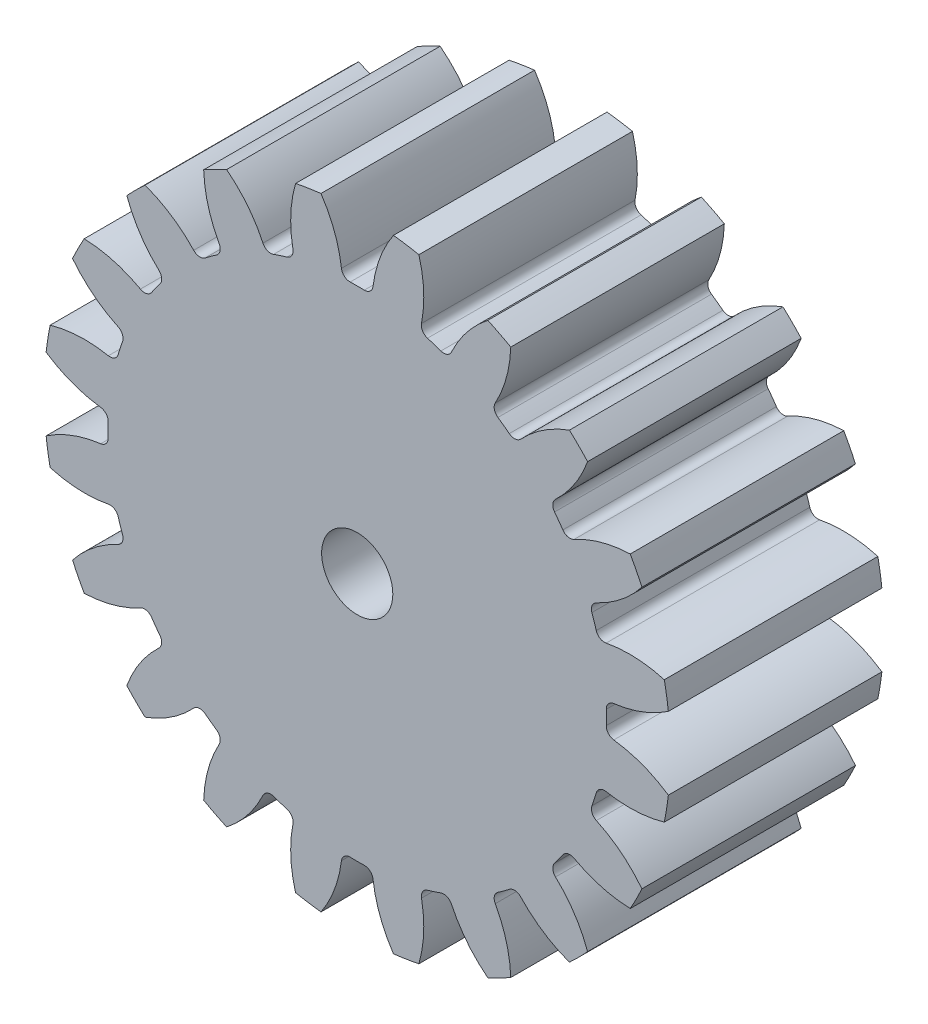
SolidWorks part; units mm, degrees
material "1023 Carbon Steel Sheet (SS)"
ref_plane "Front Plane" through (0, 0, 0) normal (0, 0, 1) x (1, 0, 0)
ref_plane "Top Plane" through (0, 0, 0) normal (0, 1, 0) x (1, 0, 0)
ref_plane "Right Plane" through (0, 0, 0) normal (1, 0, 0) x (0, 0, -1)
sketch "skBase" plane through (0, 0, 0) normal (0, 0, 1) x (1, 0, 0)
  circle A0 centre (0, 0) radius 20
  circle A1 centre (0, 0) radius 22
  circle A2 centre (0, 0) radius 17.5
  dimension "D1" = 40
  dimension "D3" = 4.5
extrude "Base" add sketch "skBase" along normal mid plane 15 contours A1
sketch "skToothProfile" plane through (0, 0, 0) normal (0, 0, 1) x (1, 0, 0)
  line L0 (0, 0) -> (0, 22) construction
  line L1 (-1.5692, 19.9383) -> (1.5692, 19.9383) construction
  line L2 (-1.0563, 17.4681) -> (0, 0) construction
  line L3 (0, 15.6271) -> (-2.6287, 22.8493) construction
  line L4 (0, 0) -> (3.4416, 21.7291) construction
  line L5 (1.5692, 19.9383) -> (4.6689, 19.4474) construction
  circle A0 centre (0, 0) radius 22 construction
  arc A1 (-1.0563, 17.4681) -> (-3.258, 22.7681) centre (-9.8105, 16.9387) ccw
  arc A2 (1.0563, 17.4681) -> (3.258, 22.7681) centre (9.8105, 16.9387) cw
  circle A3 centre (0, 0) radius 17.5 construction
  arc A4 (1.0563, 17.4681) -> (-1.0563, 17.4681) centre (0, 0) ccw
  circle A5 centre (0, 0) radius 20 construction
  circle A6 centre (0, 0) radius 22 construction
  circle A7 centre (0, 0) radius 23
  arc A8 (3.258, 22.7681) -> (-3.258, 22.7681) centre (0, 0) ccw
  dimension "D2" = 20
  dimension "D3" = 9
  dimension "D1" = 1
extrude "ToothProfile" cut sketch "skToothProfile" against normal through all and the other way through all
fillet "FilletToothProfile" radius 0.6 2 edges at (1.0563, 17.4681, 0) (-1.0563, 17.4681, 0)
pattern_circular "CirPatternTeeth" count 20 over 360 about axis through (0, 0, 0) along (0, 0, 1) of "ToothProfile", "FilletToothProfile"
sketch "skChaveta" plane through (0, 0, 7.5) normal (0, 0, 1) x (1, 0, 0)
  line L0 (0, 2.5) -> (0, 0) construction
  circle A0 centre (0, 0) radius 2.5
  dimension "D1" = 5
extrude "Chaveta" cut sketch "skChaveta" against normal through all
sketch "skRebaixo" plane through (0, 0, 7.5) normal (0, 0, 1) x (1, 0, 0)
  circle A0 centre (0, 0) radius 21.5
  circle A1 centre (0, 0) radius 7.5
  dimension "D1" = 43
  dimension "D2" = 15
sketch "Sketch4" plane through (0, 0, -7.5) normal (0, 0, -1) x (-1, 0, 0)
  circle A0 centre (0, 0) radius 17.5
  arc A5 (-2.5459, 21.8522) -> (-4.3314, 21.5694) centre (0, 0) ccw
  arc A6 (-2.5459, 21.8522) -> (-4.3314, 21.5694) centre (0, 0) ccw
  arc A7 (-18.0189, -1.107) -> (-21.8522, -2.5459) centre (-16.9387, -9.8105) ccw
  arc A8 (-18.0189, -1.107) -> (-21.8522, -2.5459) centre (-16.9387, -9.8105) ccw
  arc A9 (-21.5694, -4.3314) -> (-17.4791, -4.5153) centre (-19.1413, 4.096) ccw
  arc A10 (-21.5694, -4.3314) -> (-17.4791, -4.5153) centre (-19.1413, 4.096) ccw
  arc A127 (-19.996, -9.174) -> (-19.1752, -10.7848) centre (0, 0) ccw
  arc A128 (-19.996, -9.174) -> (-19.1752, -10.7848) centre (0, 0) ccw
  arc A129 (-16.1824, -14.904) -> (-14.904, -16.1824) centre (0, 0) ccw
  arc A130 (-16.1824, -14.904) -> (-14.904, -16.1824) centre (0, 0) ccw
  arc A131 (-10.7848, -19.1752) -> (-9.174, -19.996) centre (0, 0) ccw
  arc A132 (-10.7848, -19.1752) -> (-9.174, -19.996) centre (0, 0) ccw
  arc A133 (-4.3314, -21.5694) -> (-2.5459, -21.8522) centre (0, 0) ccw
  arc A134 (-4.3314, -21.5694) -> (-2.5459, -21.8522) centre (0, 0) ccw
  arc A135 (2.5459, -21.8522) -> (4.3314, -21.5694) centre (0, 0) ccw
  arc A136 (2.5459, -21.8522) -> (4.3314, -21.5694) centre (0, 0) ccw
  arc A137 (9.174, -19.996) -> (10.7848, -19.1752) centre (0, 0) ccw
  arc A138 (9.174, -19.996) -> (10.7848, -19.1752) centre (0, 0) ccw
  arc A139 (14.904, -16.1824) -> (16.1824, -14.904) centre (0, 0) ccw
  arc A140 (14.904, -16.1824) -> (16.1824, -14.904) centre (0, 0) ccw
  arc A141 (19.1752, -10.7848) -> (19.996, -9.174) centre (0, 0) ccw
  arc A142 (19.1752, -10.7848) -> (19.996, -9.174) centre (0, 0) ccw
  arc A143 (21.5694, -4.3314) -> (21.8522, -2.5459) centre (0, 0) ccw
  arc A144 (21.5694, -4.3314) -> (21.8522, -2.5459) centre (0, 0) ccw
  arc A145 (21.8522, 2.5459) -> (21.5694, 4.3314) centre (0, 0) ccw
  arc A146 (21.8522, 2.5459) -> (21.5694, 4.3314) centre (0, 0) ccw
  arc A147 (19.996, 9.174) -> (19.1752, 10.7848) centre (0, 0) ccw
  arc A148 (19.996, 9.174) -> (19.1752, 10.7848) centre (0, 0) ccw
  arc A149 (16.1824, 14.904) -> (14.904, 16.1824) centre (0, 0) ccw
  arc A150 (16.1824, 14.904) -> (14.904, 16.1824) centre (0, 0) ccw
  arc A151 (10.7848, 19.1752) -> (9.174, 19.996) centre (0, 0) ccw
  arc A152 (10.7848, 19.1752) -> (9.174, 19.996) centre (0, 0) ccw
  arc A153 (4.3314, 21.5694) -> (2.5459, 21.8522) centre (0, 0) ccw
  arc A154 (4.3314, 21.5694) -> (2.5459, 21.8522) centre (0, 0) ccw
  arc A155 (-9.174, 19.996) -> (-10.7848, 19.1752) centre (0, 0) ccw
  arc A156 (-9.174, 19.996) -> (-10.7848, 19.1752) centre (0, 0) ccw
  arc A157 (-14.904, 16.1824) -> (-16.1824, 14.904) centre (0, 0) ccw
  arc A158 (-14.904, 16.1824) -> (-16.1824, 14.904) centre (0, 0) ccw
  arc A159 (-19.1752, 10.7848) -> (-19.996, 9.174) centre (0, 0) ccw
  arc A160 (-19.1752, 10.7848) -> (-19.996, 9.174) centre (0, 0) ccw
  arc A161 (-21.5694, 4.3314) -> (-21.8522, 2.5459) centre (0, 0) ccw
  arc A162 (-21.5694, 4.3314) -> (-21.8522, 2.5459) centre (0, 0) ccw
  arc A163 (-4.3314, 21.5694) -> (-4.5153, 17.4791) centre (4.096, 19.1413) ccw
  arc A164 (-4.3314, 21.5694) -> (-4.5153, 17.4791) centre (4.096, 19.1413) ccw
  arc A165 (-4.9352, 16.7897) -> (-4.5153, 17.4791) centre (-5.1044, 17.3653) ccw
  arc A166 (-4.9352, 16.7897) -> (-4.5153, 17.4791) centre (-5.1044, 17.3653) ccw
  arc A167 (-4.9352, 16.7897) -> (-5.8761, 16.484) centre (0, 0) ccw
  arc A168 (-4.9352, 16.7897) -> (-5.8761, 16.484) centre (0, 0) ccw
  arc A169 (-6.621, 16.7949) -> (-5.8761, 16.484) centre (-6.0775, 17.0492) ccw
  arc A170 (-6.621, 16.7949) -> (-5.8761, 16.484) centre (-6.0775, 17.0492) ccw
  arc A171 (-6.621, 16.7949) -> (-9.174, 19.996) centre (-14.5647, 13.0781) ccw
  arc A172 (-6.621, 16.7949) -> (-9.174, 19.996) centre (-14.5647, 13.0781) ccw
  arc A173 (-10.7848, 19.1752) -> (-9.6956, 15.2283) centre (-2.0195, 19.4702) ccw
  arc A174 (-10.7848, 19.1752) -> (-9.6956, 15.2283) centre (-2.0195, 19.4702) ccw
  arc A175 (-9.882, 14.4429) -> (-9.6956, 15.2283) centre (-10.2208, 14.9381) ccw
  arc A176 (-9.882, 14.4429) -> (-9.6956, 15.2283) centre (-10.2208, 14.9381) ccw
  arc A177 (-9.882, 14.4429) -> (-10.6823, 13.8614) centre (0, 0) ccw
  arc A178 (-9.882, 14.4429) -> (-10.6823, 13.8614) centre (0, 0) ccw
  arc A179 (-11.4868, 13.9269) -> (-10.6823, 13.8614) centre (-11.0486, 14.3366) ccw
  arc A180 (-11.4868, 13.9269) -> (-10.6823, 13.8614) centre (-11.0486, 14.3366) ccw
  arc A181 (-11.4868, 13.9269) -> (-14.904, 16.1824) centre (-17.8932, 7.9372) ccw
  arc A182 (-11.4868, 13.9269) -> (-14.904, 16.1824) centre (-17.8932, 7.9372) ccw
  arc A183 (-16.1824, 14.904) -> (-13.9269, 11.4868) centre (-7.9372, 17.8932) ccw
  arc A184 (-16.1824, 14.904) -> (-13.9269, 11.4868) centre (-7.9372, 17.8932) ccw
  arc A185 (-13.8614, 10.6823) -> (-13.9269, 11.4868) centre (-14.3366, 11.0486) ccw
  arc A186 (-13.8614, 10.6823) -> (-13.9269, 11.4868) centre (-14.3366, 11.0486) ccw
  arc A187 (-13.8614, 10.6823) -> (-14.4429, 9.882) centre (0, 0) ccw
  arc A188 (-13.8614, 10.6823) -> (-14.4429, 9.882) centre (0, 0) ccw
  arc A189 (-15.2283, 9.6956) -> (-14.4429, 9.882) centre (-14.9381, 10.2208) ccw
  arc A190 (-15.2283, 9.6956) -> (-14.4429, 9.882) centre (-14.9381, 10.2208) ccw
  arc A191 (-15.2283, 9.6956) -> (-19.1752, 10.7848) centre (-19.4702, 2.0195) ccw
  arc A192 (-15.2283, 9.6956) -> (-19.1752, 10.7848) centre (-19.4702, 2.0195) ccw
  arc A193 (-19.996, 9.174) -> (-16.7949, 6.621) centre (-13.0781, 14.5647) ccw
  arc A194 (-19.996, 9.174) -> (-16.7949, 6.621) centre (-13.0781, 14.5647) ccw
  arc A195 (-16.484, 5.8761) -> (-16.7949, 6.621) centre (-17.0492, 6.0775) ccw
  arc A196 (-16.484, 5.8761) -> (-16.7949, 6.621) centre (-17.0492, 6.0775) ccw
  arc A197 (-16.484, 5.8761) -> (-16.7897, 4.9352) centre (0, 0) ccw
  arc A198 (-16.484, 5.8761) -> (-16.7897, 4.9352) centre (0, 0) ccw
  arc A199 (-17.4791, 4.5153) -> (-16.7897, 4.9352) centre (-17.3653, 5.1044) ccw
  arc A200 (-17.4791, 4.5153) -> (-16.7897, 4.9352) centre (-17.3653, 5.1044) ccw
  arc A201 (-17.4791, 4.5153) -> (-21.5694, 4.3314) centre (-19.1413, -4.096) ccw
  arc A202 (-17.4791, 4.5153) -> (-21.5694, 4.3314) centre (-19.1413, -4.096) ccw
  arc A203 (-21.8522, 2.5459) -> (-18.0189, 1.107) centre (-16.9387, 9.8105) ccw
  arc A204 (-21.8522, 2.5459) -> (-18.0189, 1.107) centre (-16.9387, 9.8105) ccw
  arc A205 (-17.493, 0.4946) -> (-18.0189, 1.107) centre (-18.0928, 0.5116) ccw
  arc A206 (-17.493, 0.4946) -> (-18.0189, 1.107) centre (-18.0928, 0.5116) ccw
  arc A207 (-17.493, 0.4946) -> (-17.493, -0.4946) centre (0, 0) ccw
  arc A208 (-17.493, 0.4946) -> (-17.493, -0.4946) centre (0, 0) ccw
  arc A209 (-18.0189, -1.107) -> (-17.493, -0.4946) centre (-18.0928, -0.5116) ccw
  arc A210 (-18.0189, -1.107) -> (-17.493, -0.4946) centre (-18.0928, -0.5116) ccw
  arc A211 (-16.7897, -4.9352) -> (-17.4791, -4.5153) centre (-17.3653, -5.1044) ccw
  arc A212 (-16.7897, -4.9352) -> (-17.4791, -4.5153) centre (-17.3653, -5.1044) ccw
  arc A213 (-16.7897, -4.9352) -> (-16.484, -5.8761) centre (0, 0) ccw
  arc A214 (-16.7897, -4.9352) -> (-16.484, -5.8761) centre (0, 0) ccw
  arc A215 (-16.7949, -6.621) -> (-16.484, -5.8761) centre (-17.0492, -6.0775) ccw
  arc A216 (-16.7949, -6.621) -> (-16.484, -5.8761) centre (-17.0492, -6.0775) ccw
  arc A217 (-16.7949, -6.621) -> (-19.996, -9.174) centre (-13.0781, -14.5647) ccw
  arc A218 (-16.7949, -6.621) -> (-19.996, -9.174) centre (-13.0781, -14.5647) ccw
  arc A219 (-19.1752, -10.7848) -> (-15.2283, -9.6956) centre (-19.4702, -2.0195) ccw
  arc A220 (-19.1752, -10.7848) -> (-15.2283, -9.6956) centre (-19.4702, -2.0195) ccw
  arc A221 (-14.4429, -9.882) -> (-15.2283, -9.6956) centre (-14.9381, -10.2208) ccw
  arc A222 (-14.4429, -9.882) -> (-15.2283, -9.6956) centre (-14.9381, -10.2208) ccw
  arc A223 (-14.4429, -9.882) -> (-13.8614, -10.6823) centre (0, 0) ccw
  arc A224 (-14.4429, -9.882) -> (-13.8614, -10.6823) centre (0, 0) ccw
  arc A225 (-13.9269, -11.4868) -> (-13.8614, -10.6823) centre (-14.3366, -11.0486) ccw
  arc A226 (-13.9269, -11.4868) -> (-13.8614, -10.6823) centre (-14.3366, -11.0486) ccw
  arc A227 (-13.9269, -11.4868) -> (-16.1824, -14.904) centre (-7.9372, -17.8932) ccw
  arc A228 (-13.9269, -11.4868) -> (-16.1824, -14.904) centre (-7.9372, -17.8932) ccw
  arc A229 (-14.904, -16.1824) -> (-11.4868, -13.9269) centre (-17.8932, -7.9372) ccw
  arc A230 (-14.904, -16.1824) -> (-11.4868, -13.9269) centre (-17.8932, -7.9372) ccw
  arc A231 (-10.6823, -13.8614) -> (-11.4868, -13.9269) centre (-11.0486, -14.3366) ccw
  arc A232 (-10.6823, -13.8614) -> (-11.4868, -13.9269) centre (-11.0486, -14.3366) ccw
  arc A233 (-10.6823, -13.8614) -> (-9.882, -14.4429) centre (0, 0) ccw
  arc A234 (-10.6823, -13.8614) -> (-9.882, -14.4429) centre (0, 0) ccw
  arc A235 (-9.6956, -15.2283) -> (-9.882, -14.4429) centre (-10.2208, -14.9381) ccw
  arc A236 (-9.6956, -15.2283) -> (-9.882, -14.4429) centre (-10.2208, -14.9381) ccw
  arc A237 (-9.6956, -15.2283) -> (-10.7848, -19.1752) centre (-2.0195, -19.4702) ccw
  arc A238 (-9.6956, -15.2283) -> (-10.7848, -19.1752) centre (-2.0195, -19.4702) ccw
  arc A239 (-9.174, -19.996) -> (-6.621, -16.7949) centre (-14.5647, -13.0781) ccw
  arc A240 (-9.174, -19.996) -> (-6.621, -16.7949) centre (-14.5647, -13.0781) ccw
  arc A241 (-5.8761, -16.484) -> (-6.621, -16.7949) centre (-6.0775, -17.0492) ccw
  arc A242 (-5.8761, -16.484) -> (-6.621, -16.7949) centre (-6.0775, -17.0492) ccw
  arc A243 (-5.8761, -16.484) -> (-4.9352, -16.7897) centre (0, 0) ccw
  arc A244 (-5.8761, -16.484) -> (-4.9352, -16.7897) centre (0, 0) ccw
  arc A245 (-4.5153, -17.4791) -> (-4.9352, -16.7897) centre (-5.1044, -17.3653) ccw
  arc A246 (-4.5153, -17.4791) -> (-4.9352, -16.7897) centre (-5.1044, -17.3653) ccw
  arc A247 (-4.5153, -17.4791) -> (-4.3314, -21.5694) centre (4.096, -19.1413) ccw
  arc A248 (-4.5153, -17.4791) -> (-4.3314, -21.5694) centre (4.096, -19.1413) ccw
  arc A249 (-2.5459, -21.8522) -> (-1.107, -18.0189) centre (-9.8105, -16.9387) ccw
  arc A250 (-2.5459, -21.8522) -> (-1.107, -18.0189) centre (-9.8105, -16.9387) ccw
  arc A251 (-0.4946, -17.493) -> (-1.107, -18.0189) centre (-0.5116, -18.0928) ccw
  arc A252 (-0.4946, -17.493) -> (-1.107, -18.0189) centre (-0.5116, -18.0928) ccw
  arc A253 (-0.4946, -17.493) -> (0.4946, -17.493) centre (0, 0) ccw
  arc A254 (-0.4946, -17.493) -> (0.4946, -17.493) centre (0, 0) ccw
  arc A255 (1.107, -18.0189) -> (0.4946, -17.493) centre (0.5116, -18.0928) ccw
  arc A256 (1.107, -18.0189) -> (0.4946, -17.493) centre (0.5116, -18.0928) ccw
  arc A257 (1.107, -18.0189) -> (2.5459, -21.8522) centre (9.8105, -16.9387) ccw
  arc A258 (1.107, -18.0189) -> (2.5459, -21.8522) centre (9.8105, -16.9387) ccw
  arc A259 (4.3314, -21.5694) -> (4.5153, -17.4791) centre (-4.096, -19.1413) ccw
  arc A260 (4.3314, -21.5694) -> (4.5153, -17.4791) centre (-4.096, -19.1413) ccw
  arc A261 (4.9352, -16.7897) -> (4.5153, -17.4791) centre (5.1044, -17.3653) ccw
  arc A262 (4.9352, -16.7897) -> (4.5153, -17.4791) centre (5.1044, -17.3653) ccw
  arc A263 (4.9352, -16.7897) -> (5.8761, -16.484) centre (0, 0) ccw
  arc A264 (4.9352, -16.7897) -> (5.8761, -16.484) centre (0, 0) ccw
  arc A265 (6.621, -16.7949) -> (5.8761, -16.484) centre (6.0775, -17.0492) ccw
  arc A266 (6.621, -16.7949) -> (5.8761, -16.484) centre (6.0775, -17.0492) ccw
  arc A267 (6.621, -16.7949) -> (9.174, -19.996) centre (14.5647, -13.0781) ccw
  arc A268 (6.621, -16.7949) -> (9.174, -19.996) centre (14.5647, -13.0781) ccw
  arc A269 (10.7848, -19.1752) -> (9.6956, -15.2283) centre (2.0195, -19.4702) ccw
  arc A270 (10.7848, -19.1752) -> (9.6956, -15.2283) centre (2.0195, -19.4702) ccw
  arc A271 (9.882, -14.4429) -> (9.6956, -15.2283) centre (10.2208, -14.9381) ccw
  arc A272 (9.882, -14.4429) -> (9.6956, -15.2283) centre (10.2208, -14.9381) ccw
  arc A273 (9.882, -14.4429) -> (10.6823, -13.8614) centre (0, 0) ccw
  arc A274 (9.882, -14.4429) -> (10.6823, -13.8614) centre (0, 0) ccw
  arc A275 (11.4868, -13.9269) -> (10.6823, -13.8614) centre (11.0486, -14.3366) ccw
  arc A276 (11.4868, -13.9269) -> (10.6823, -13.8614) centre (11.0486, -14.3366) ccw
  arc A277 (11.4868, -13.9269) -> (14.904, -16.1824) centre (17.8932, -7.9372) ccw
  arc A278 (11.4868, -13.9269) -> (14.904, -16.1824) centre (17.8932, -7.9372) ccw
  arc A279 (16.1824, -14.904) -> (13.9269, -11.4868) centre (7.9372, -17.8932) ccw
  arc A280 (16.1824, -14.904) -> (13.9269, -11.4868) centre (7.9372, -17.8932) ccw
  arc A281 (13.8614, -10.6823) -> (13.9269, -11.4868) centre (14.3366, -11.0486) ccw
  arc A282 (13.8614, -10.6823) -> (13.9269, -11.4868) centre (14.3366, -11.0486) ccw
  arc A283 (13.8614, -10.6823) -> (14.4429, -9.882) centre (0, 0) ccw
  arc A284 (13.8614, -10.6823) -> (14.4429, -9.882) centre (0, 0) ccw
  arc A285 (15.2283, -9.6956) -> (14.4429, -9.882) centre (14.9381, -10.2208) ccw
  arc A286 (15.2283, -9.6956) -> (14.4429, -9.882) centre (14.9381, -10.2208) ccw
  arc A287 (15.2283, -9.6956) -> (19.1752, -10.7848) centre (19.4702, -2.0195) ccw
  arc A288 (15.2283, -9.6956) -> (19.1752, -10.7848) centre (19.4702, -2.0195) ccw
  arc A289 (19.996, -9.174) -> (16.7949, -6.621) centre (13.0781, -14.5647) ccw
  arc A290 (19.996, -9.174) -> (16.7949, -6.621) centre (13.0781, -14.5647) ccw
  arc A291 (16.484, -5.8761) -> (16.7949, -6.621) centre (17.0492, -6.0775) ccw
  arc A292 (16.484, -5.8761) -> (16.7949, -6.621) centre (17.0492, -6.0775) ccw
  arc A293 (16.484, -5.8761) -> (16.7897, -4.9352) centre (0, 0) ccw
  arc A294 (16.484, -5.8761) -> (16.7897, -4.9352) centre (0, 0) ccw
  arc A295 (17.4791, -4.5153) -> (16.7897, -4.9352) centre (17.3653, -5.1044) ccw
  arc A296 (17.4791, -4.5153) -> (16.7897, -4.9352) centre (17.3653, -5.1044) ccw
  arc A297 (17.4791, -4.5153) -> (21.5694, -4.3314) centre (19.1413, 4.096) ccw
  arc A298 (17.4791, -4.5153) -> (21.5694, -4.3314) centre (19.1413, 4.096) ccw
  arc A299 (21.8522, -2.5459) -> (18.0189, -1.107) centre (16.9387, -9.8105) ccw
  arc A300 (21.8522, -2.5459) -> (18.0189, -1.107) centre (16.9387, -9.8105) ccw
  arc A301 (17.493, -0.4946) -> (18.0189, -1.107) centre (18.0928, -0.5116) ccw
  arc A302 (17.493, -0.4946) -> (18.0189, -1.107) centre (18.0928, -0.5116) ccw
  arc A303 (17.493, -0.4946) -> (17.493, 0.4946) centre (0, 0) ccw
  arc A304 (17.493, -0.4946) -> (17.493, 0.4946) centre (0, 0) ccw
  arc A305 (18.0189, 1.107) -> (17.493, 0.4946) centre (18.0928, 0.5116) ccw
  arc A306 (18.0189, 1.107) -> (17.493, 0.4946) centre (18.0928, 0.5116) ccw
  arc A307 (18.0189, 1.107) -> (21.8522, 2.5459) centre (16.9387, 9.8105) ccw
  arc A308 (18.0189, 1.107) -> (21.8522, 2.5459) centre (16.9387, 9.8105) ccw
  arc A309 (21.5694, 4.3314) -> (17.4791, 4.5153) centre (19.1413, -4.096) ccw
  arc A310 (21.5694, 4.3314) -> (17.4791, 4.5153) centre (19.1413, -4.096) ccw
  arc A311 (-21.8522, -2.5459) -> (-21.5694, -4.3314) centre (0, 0) ccw
  arc A312 (-21.8522, -2.5459) -> (-21.5694, -4.3314) centre (0, 0) ccw
  arc A313 (16.7897, 4.9352) -> (17.4791, 4.5153) centre (17.3653, 5.1044) ccw
  arc A314 (16.7897, 4.9352) -> (17.4791, 4.5153) centre (17.3653, 5.1044) ccw
  arc A315 (16.7897, 4.9352) -> (16.484, 5.8761) centre (0, 0) ccw
  arc A316 (16.7897, 4.9352) -> (16.484, 5.8761) centre (0, 0) ccw
  arc A317 (16.7949, 6.621) -> (16.484, 5.8761) centre (17.0492, 6.0775) ccw
  arc A318 (16.7949, 6.621) -> (16.484, 5.8761) centre (17.0492, 6.0775) ccw
  arc A319 (16.7949, 6.621) -> (19.996, 9.174) centre (13.0781, 14.5647) ccw
  arc A320 (16.7949, 6.621) -> (19.996, 9.174) centre (13.0781, 14.5647) ccw
  arc A321 (19.1752, 10.7848) -> (15.2283, 9.6956) centre (19.4702, 2.0195) ccw
  arc A322 (19.1752, 10.7848) -> (15.2283, 9.6956) centre (19.4702, 2.0195) ccw
  arc A323 (14.4429, 9.882) -> (15.2283, 9.6956) centre (14.9381, 10.2208) ccw
  arc A324 (14.4429, 9.882) -> (15.2283, 9.6956) centre (14.9381, 10.2208) ccw
  arc A325 (14.4429, 9.882) -> (13.8614, 10.6823) centre (0, 0) ccw
  arc A326 (14.4429, 9.882) -> (13.8614, 10.6823) centre (0, 0) ccw
  arc A327 (13.9269, 11.4868) -> (13.8614, 10.6823) centre (14.3366, 11.0486) ccw
  arc A328 (13.9269, 11.4868) -> (13.8614, 10.6823) centre (14.3366, 11.0486) ccw
  arc A329 (13.9269, 11.4868) -> (16.1824, 14.904) centre (7.9372, 17.8932) ccw
  arc A330 (13.9269, 11.4868) -> (16.1824, 14.904) centre (7.9372, 17.8932) ccw
  arc A331 (14.904, 16.1824) -> (11.4868, 13.9269) centre (17.8932, 7.9372) ccw
  arc A332 (14.904, 16.1824) -> (11.4868, 13.9269) centre (17.8932, 7.9372) ccw
  arc A333 (10.6823, 13.8614) -> (11.4868, 13.9269) centre (11.0486, 14.3366) ccw
  arc A334 (10.6823, 13.8614) -> (11.4868, 13.9269) centre (11.0486, 14.3366) ccw
  arc A335 (10.6823, 13.8614) -> (9.882, 14.4429) centre (0, 0) ccw
  arc A336 (10.6823, 13.8614) -> (9.882, 14.4429) centre (0, 0) ccw
  arc A337 (9.6956, 15.2283) -> (9.882, 14.4429) centre (10.2208, 14.9381) ccw
  arc A338 (9.6956, 15.2283) -> (9.882, 14.4429) centre (10.2208, 14.9381) ccw
  arc A339 (9.6956, 15.2283) -> (10.7848, 19.1752) centre (2.0195, 19.4702) ccw
  arc A340 (9.6956, 15.2283) -> (10.7848, 19.1752) centre (2.0195, 19.4702) ccw
  arc A341 (9.174, 19.996) -> (6.621, 16.7949) centre (14.5647, 13.0781) ccw
  arc A342 (9.174, 19.996) -> (6.621, 16.7949) centre (14.5647, 13.0781) ccw
  arc A343 (5.8761, 16.484) -> (6.621, 16.7949) centre (6.0775, 17.0492) ccw
  arc A344 (5.8761, 16.484) -> (6.621, 16.7949) centre (6.0775, 17.0492) ccw
  arc A345 (5.8761, 16.484) -> (4.9352, 16.7897) centre (0, 0) ccw
  arc A346 (5.8761, 16.484) -> (4.9352, 16.7897) centre (0, 0) ccw
  arc A347 (4.5153, 17.4791) -> (4.9352, 16.7897) centre (5.1044, 17.3653) ccw
  arc A348 (4.5153, 17.4791) -> (4.9352, 16.7897) centre (5.1044, 17.3653) ccw
  arc A349 (4.5153, 17.4791) -> (4.3314, 21.5694) centre (-4.096, 19.1413) ccw
  arc A350 (4.5153, 17.4791) -> (4.3314, 21.5694) centre (-4.096, 19.1413) ccw
  arc A351 (2.5459, 21.8522) -> (1.107, 18.0189) centre (9.8105, 16.9387) ccw
  arc A352 (2.5459, 21.8522) -> (1.107, 18.0189) centre (9.8105, 16.9387) ccw
  arc A353 (0.4946, 17.493) -> (1.107, 18.0189) centre (0.5116, 18.0928) ccw
  arc A354 (0.4946, 17.493) -> (1.107, 18.0189) centre (0.5116, 18.0928) ccw
  arc A355 (0.4946, 17.493) -> (-0.4946, 17.493) centre (0, 0) ccw
  arc A356 (0.4946, 17.493) -> (-0.4946, 17.493) centre (0, 0) ccw
  arc A357 (-1.107, 18.0189) -> (-0.4946, 17.493) centre (-0.5116, 18.0928) ccw
  arc A358 (-1.107, 18.0189) -> (-0.4946, 17.493) centre (-0.5116, 18.0928) ccw
  arc A359 (-1.107, 18.0189) -> (-2.5459, 21.8522) centre (-9.8105, 16.9387) ccw
  arc A360 (-1.107, 18.0189) -> (-2.5459, 21.8522) centre (-9.8105, 16.9387) ccw
  dimension "D1" = 0
sketch "Sketch6" plane through (0, 0, -7.5) normal (0, 0, -1) x (-1, 0, 0)
  circle A0 centre (0, 0) radius 20 construction
  dimension "D1" = 40
equation "\"Module\"= 2mm"
equation "\"Number_Of_Teeth\" = 20"
equation "\"D1@skBase\"=\"Module\" * \"Number_Of_Teeth\""
equation "\"D2@skBase\"=\"Module\""
equation "\"D3@skBase\"=\"Module\" * if( \"Module\" >=1.25, 2.25, 2.4)"
equation "\"Pressure_Angle\"= 20deg"
equation "\"D2@skToothProfile\"=\"Pressure_Angle\""
equation "\"D3@skToothProfile\"=180 / \"Number_Of_Teeth\""
equation "\"D1@FilletToothProfile\"= 0.3 * \"Module\""
equation "\"D1@CirPatternTeeth\"=\"Number_Of_Teeth\""
equation "\"Width\"= 15mm"
equation "\"D1@Base\"=\"Width\""
